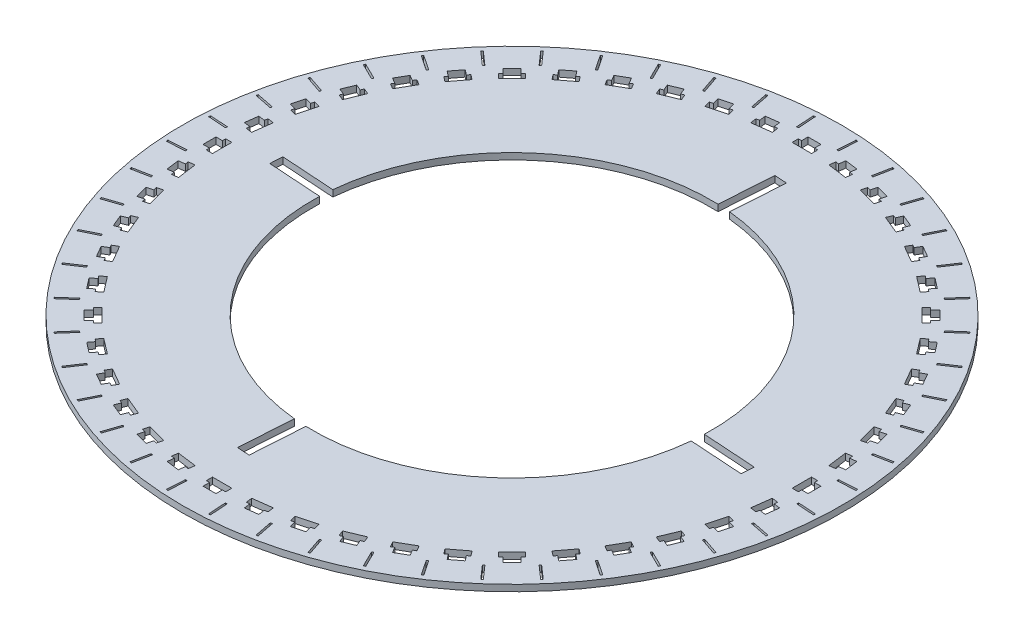
SolidWorks part; units mm, degrees
ref_plane "前视基准面" through (0, 0, 0) normal (0, 0, 1) x (1, 0, 0)
ref_plane "上视基准面" through (0, 0, 0) normal (0, 1, 0) x (1, 0, 0)
ref_plane "右视基准面" through (0, 0, 0) normal (1, 0, 0) x (0, 0, -1)
sketch "草图1" plane through (0, 0, 0) normal (0, 1, 0) x (1, 0, 0)
  circle A0 centre (0, 0) radius 154.62
  circle A1 centre (0, 0) radius 254.62
  dimension "D1" = 509.24
  dimension "D2" = 100
extrude "凸台-拉伸1" add sketch "草图1" along normal blind 5
sketch "草图2" plane through (0, 5, 0) normal (0, 1, 0) x (1, 0, 0)
  line L0 (0, 0) -> (0, -254.62) construction
  line L5 (-5, -234.62) -> (5, -234.62)
  line L6 (-5, -234.62) -> (-5, -229.62)
  line L7 (-45.453, -254.62) -> (45.453, -254.62) construction
  line L8 (5, -234.62) -> (5, -229.62)
  line L9 (-5, -229.62) -> (5, -229.62)
  line L10 (-5, -234.62) -> (5, -229.62) construction
  line L11 (5, -234.62) -> (-5, -229.62) construction
  line L13 (-7.5, -224.82) -> (7.5, -224.82)
  line L14 (-7.5, -224.82) -> (-7.5, -229.62)
  line L15 (-7.5, -229.62) -> (7.5, -229.62)
  line L16 (7.5, -224.82) -> (7.5, -229.62)
  line L17 (-7.5, -224.82) -> (7.5, -229.62) construction
  line L18 (-7.5, -229.62) -> (7.5, -224.82) construction
  circle A0 centre (0, 0) radius 254.62 construction
  point P0 (0, -227.22)
  point P1 (0, -232.12)
  dimension "D1" = 20
  dimension "D2" = 10
  dimension "D3" = 5
  dimension "D4" = 15
  dimension "D5" = 4.8
extrude "切除-拉伸1" cut sketch "草图2" against normal blind 5 contours L16 L13 L14 L15 L9 | L9 L6 L5 L8
pattern_circular "阵列(圆周)1" count 48 over 360 about axis through (0, 0, 0) along (0, 1, 0) of "切除-拉伸1"
sketch "草图3" plane through (0, 5, 0) normal (0, 1, 0) x (1, 0, 0)
  line L0 (0, 0) -> (0, -270.2724) construction
  line L1 (0, 0) -> (39.1441, -297.329) construction
  line L2 (21.9091, -223.8756) -> (36.7807, -221.9177) construction
  line L3 (0, 0) -> (18.2234, -278.0352) construction
  line L4 (12.971, -197.8995) -> (0, -197.8995) construction
  line L5 (12.971, -197.8995) -> (25.8311, -196.2065) construction
  line L6 (15.7582, -251.127) -> (14.8426, -237.157)
  line L7 (15.7582, -251.127) -> (17.1552, -251.0355)
  line L8 (14.8426, -237.157) -> (16.2396, -237.0655)
  line L9 (17.1552, -251.0355) -> (16.2396, -237.0655)
  line L10 (15.7582, -251.127) -> (16.2396, -237.0655) construction
  line L11 (14.8426, -237.157) -> (17.1552, -251.0355) construction
  line L12 (5.7103, -254.7921) -> (25.8256, -253.4736) construction
  circle A0 centre (0, 0) radius 254.62 construction
  point P11 (15.9989, -244.0962)
  dimension "D1" = 1.4
  dimension "D2" = 14
  dimension "D3" = 10
extrude "切除-拉伸2" cut sketch "草图3" against normal up to next (5 mm away)
pattern_circular "阵列(圆周)2" count 48 every 7.5 about axis through (0, 0, 0) along (0, 1, 0) of "切除-拉伸2"
sketch "草图5" plane through (0, 0, 0) normal (0, 1, 0) x (1, 0, 0)
  circle A0 centre (0, 0) radius 254.62
  circle A1 centre (0, 0) radius 255.62
  circle A2 centre (0, 0) radius 254.62 construction
  dimension "D1" = 1
extrude "凸台-拉伸3" add sketch "草图5" along normal blind 5
sketch "草图6" plane through (0, 5, 0) normal (0, 1, 0) x (1, 0, 0)
  line L0 (-205.9003, 13.4954) -> (207.6474, -13.6099) construction
  line L1 (-223.8756, 21.9091) -> (0, 0) construction
  line L2 (-195.8943, 8.0293) -> (-146.0013, 4.7591)
  line L3 (-195.8943, 8.0293) -> (-195.2664, 17.6087)
  line L4 (-195.2664, 17.6087) -> (-145.3735, 14.3386)
  line L5 (-146.0013, 4.7591) -> (-145.3735, 14.3386)
  line L6 (-195.8943, 8.0293) -> (-145.3735, 14.3386) construction
  line L7 (-195.2664, 17.6087) -> (-146.0013, 4.7591) construction
  line L8 (0, 0) -> (-224.82, 7.5) construction
  line L9 (-120.3565, 11.7784) -> (-120.7347, 7.9134) construction
  line L10 (-120.7347, 7.9134) -> (-120.8642, 4.032) construction
  point P3 (-170.6339, 11.1839)
  point P8 (-195.5803, 12.819)
  dimension "D1" = 9.6
  dimension "D2" = 25
  dimension "D3" = 196
extrude "切除-拉伸3" cut sketch "草图6" against normal up to next
pattern_circular "阵列(圆周)3" count 4 over 360 about axis through (0, 0, 0) along (0, 1, 0) of "切除-拉伸3"
